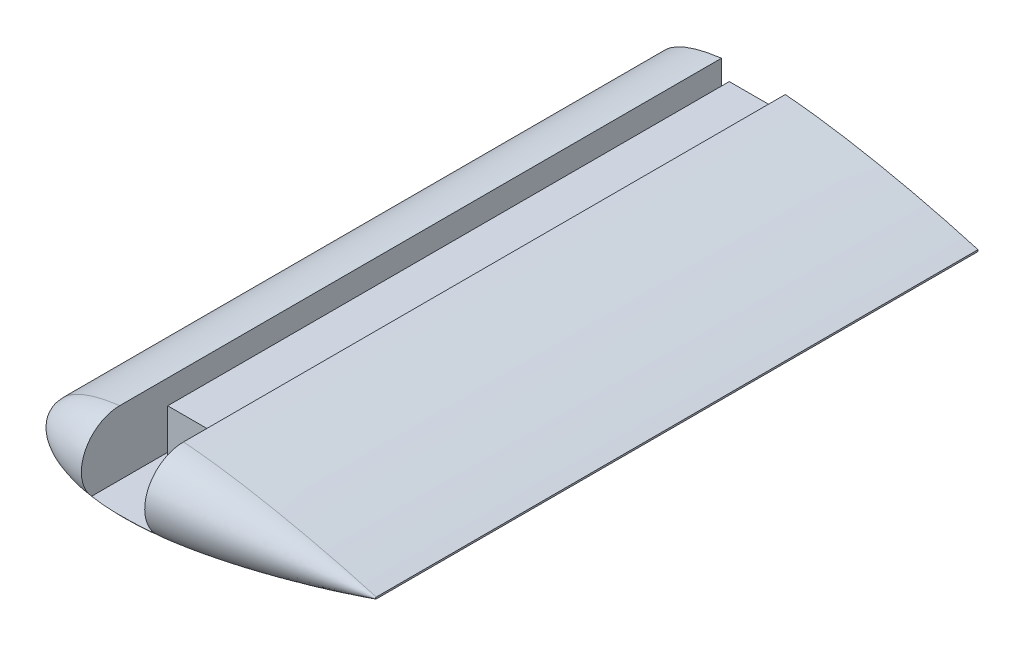
SolidWorks part; units mm, degrees
ref_plane "Спереди" through (0, 0, 0) normal (0, 0, 1) x (1, 0, 0)
ref_plane "Сверху" through (0, 0, 0) normal (0, 1, 0) x (1, 0, 0)
ref_plane "Справа" through (0, 0, 0) normal (1, 0, 0) x (0, 0, -1)
other "Configuration Table"
curve "Curve1"
  spline degree 3 poles (1, 0.0026, 0) (0.9995, 0.0028, 0) (0.9974, 0.0034, 0) (0.9928, 0.0047, 0) (0.9852, 0.0069, 0) (0.9746, 0.01, 0) (0.961, 0.0138, 0) (0.9446, 0.0183, 0) (0.9255, 0.0235, 0) (0.9037, 0.0292, 0) (0.8794, 0.0355, 0) (0.8529, 0.0421, 0) (0.8241, 0.0491, 0) (0.7933, 0.0562, 0) (0.7607, 0.0635, 0) (0.7266, 0.0709, 0) (0.691, 0.0782, 0) (0.6542, 0.0854, 0) (0.6165, 0.0923, 0) (0.5781, 0.0988, 0) (0.5392, 0.1049, 0) (0.5, 0.1104, 0) (0.4609, 0.1152, 0) (0.422, 0.1192, 0) (0.3836, 0.1222, 0) (0.3458, 0.1243, 0) (0.3091, 0.1252, 0) (0.2735, 0.1249, 0) (0.2392, 0.1234, 0) (0.2066, 0.1205, 0) (0.1758, 0.1164, 0) (0.147, 0.111, 0) (0.1203, 0.1043, 0) (0.096, 0.0965, 0) (0.0741, 0.0875, 0) (0.0549, 0.0774, 0) (0.0383, 0.0665, 0) (0.0245, 0.0546, 0) (0.0137, 0.042, 0) (0.0058, 0.0286, 0) (0.001, 0.0145, 0) (-0.0005, 0, 0) (0.001, -0.0145, 0) (0.0058, -0.0286, 0) (0.0137, -0.042, 0) (0.0245, -0.0546, 0) (0.0383, -0.0665, 0) (0.0549, -0.0774, 0) (0.0741, -0.0875, 0) (0.096, -0.0965, 0) (0.1203, -0.1043, 0) (0.147, -0.111, 0) (0.1758, -0.1164, 0) (0.2066, -0.1205, 0) (0.2392, -0.1234, 0) (0.2735, -0.1249, 0) (0.3091, -0.1252, 0) (0.3458, -0.1243, 0) (0.3836, -0.1222, 0) (0.422, -0.1192, 0) (0.4609, -0.1152, 0) (0.5, -0.1104, 0) (0.5392, -0.1049, 0) (0.5781, -0.0988, 0) (0.6165, -0.0923, 0) (0.6542, -0.0854, 0) (0.691, -0.0782, 0) (0.7266, -0.0709, 0) (0.7607, -0.0635, 0) (0.7933, -0.0562, 0) (0.8241, -0.0491, 0) (0.8529, -0.0421, 0) (0.8794, -0.0355, 0) (0.9037, -0.0292, 0) (0.9255, -0.0235, 0) (0.9446, -0.0183, 0) (0.961, -0.0138, 0) (0.9746, -0.01, 0) (0.9852, -0.0069, 0) (0.9928, -0.0047, 0) (0.9974, -0.0034, 0) (0.9995, -0.0028, 0) (1, -0.0026, 0) knots 0 0 0 0 0.000754 0.003013 0.006759 0.011967 0.018601 0.026614 0.035953 0.046555 0.058348 0.071256 0.085193 0.100071 0.115793 0.132259 0.149363 0.166997 0.185048 0.203403 0.221946 0.240561 0.259134 0.27755 0.295701 0.313483 0.330797 0.347552 0.363666 0.379065 0.393686 0.407475 0.420392 0.432406 0.443503 0.453686 0.462984 0.471456 0.479204 0.486388 0.493229 0.5 0.506771 0.513612 0.520796 0.528544 0.537016 0.546314 0.556497 0.567594 0.579608 0.592525 0.606314 0.620935 0.636334 0.652448 0.669203 0.686517 0.704299 0.72245 0.740866 0.759439 0.778054 0.796597 0.814952 0.833003 0.850637 0.867741 0.884207 0.899929 0.914807 0.928744 0.941652 0.953445 0.964047 0.973386 0.981399 0.988033 0.993241 0.996987 0.999246 1 1 1 1
sketch "Sketch2" plane through (0, 0, 0) normal (0, 0, 1) x (1, 0, 0)
  line L0 (55.999, 0.2099) -> (55.999, -0.2099) construction
  line L1 (55.999, 0) -> (-23.9777, 0) construction
  line L2 (-23.9777, 0) -> (-23.9777, 20.1567) construction
  line L3 (-7.5754, 10) -> (21.8908, 10) construction
  line L4 (55.999, 0.2099) -> (55.999, -0.2099)
  line L5 (0, 10) -> (0, -10) construction
  line L6 (55.999, -0.2099) -> (55.999, 14.9208) construction
  spline S1 degree 3 poles (55.999, 0.2099) (53.4639, 0.9505) (48.8039, 2.2339) (42.4289, 3.8199) (36.7434, 5.1209) (31.1997, 6.2872) (25.2824, 7.4075) (20.1765, 8.2452) (14.9796, 8.9749) (10.8215, 9.4486) (6.6974, 9.777) (3.6807, 9.9396) (0.7396, 10.0127) (-2.1078, 9.99) (-4.8439, 9.867) (-7.4522, 9.6409) (-9.9165, 9.3106) (-12.2218, 8.8772) (-14.354, 8.3437) (-16.3004, 7.7143) (-18.0494, 6.9954) (-19.5906, 6.1934) (-20.9154, 5.3156) (-22.0159, 4.3681) (-22.8849, 3.3565) (-23.5145, 2.285) (-23.8954, 1.1588) (-24.0187, 0) (-23.8954, -1.1588) (-23.5145, -2.285) (-22.8849, -3.3565) (-22.0159, -4.3681) (-20.9154, -5.3156) (-19.5906, -6.1934) (-18.0494, -6.9954) (-16.3004, -7.7143) (-14.354, -8.3437) (-12.2218, -8.8772) (-9.9165, -9.3106) (-7.4522, -9.6409) (-4.8439, -9.867) (-2.1078, -9.99) (0.7396, -10.0127) (3.6807, -9.9396) (7.7407, -9.7208) (12.9128, -9.2413) (19.1367, -8.4158) (25.2824, -7.4074) (31.1998, -6.2873) (37.5172, -4.9581) (44.7426, -3.2759) (51.0576, -1.6263) (54.945, -0.5178) (55.9579, -0.2219) (55.999, -0.2099) knots 0 0 0 0 0.046555 0.085193 0.115793 0.149363 0.185048 0.221946 0.240561 0.27755 0.295701 0.313483 0.330797 0.347552 0.363666 0.379065 0.393686 0.407475 0.420392 0.432406 0.443503 0.453686 0.462984 0.471456 0.479204 0.486388 0.493229 0.5 0.506771 0.513612 0.520796 0.528544 0.537016 0.546314 0.556497 0.567594 0.579608 0.592525 0.606314 0.620935 0.636334 0.652448 0.669203 0.686517 0.704299 0.740866 0.778054 0.814952 0.850637 0.884207 0.928744 0.981399 0.999246 1 1 1 1
  point P11 (0, 0)
  dimension "D1" = 20
extrude "Boss-Extrude1" add sketch "Sketch2" along normal blind 150
sketch "Sketch4" plane through (0, 0, 150) normal (0, 0, 1) x (1, 0, 0)
  line L0 (55.999, 0) -> (-23.9777, 0)
  line L1 (55.999, -0.2099) -> (55.999, 0.2099) construction
  line L3 (55.999, -0.2099) -> (55.999, 0.2099)
  line L4 (55.999, 0) -> (55.999, 0.2099)
  spline S0 degree 3 poles (55.999, 0.2099) (53.4639, 0.9505) (48.8039, 2.2339) (42.4289, 3.8199) (36.7434, 5.1209) (31.1997, 6.2872) (25.2824, 7.4075) (20.1765, 8.2452) (14.9796, 8.9749) (10.8215, 9.4486) (6.6974, 9.777) (3.6807, 9.9396) (0.7396, 10.0127) (-2.1078, 9.99) (-4.8439, 9.867) (-7.4522, 9.6409) (-9.9165, 9.3106) (-12.2218, 8.8772) (-14.354, 8.3437) (-16.3004, 7.7143) (-18.0494, 6.9954) (-19.5906, 6.1934) (-20.9154, 5.3156) (-22.0159, 4.3681) (-22.8849, 3.3565) (-23.5145, 2.285) (-23.8954, 1.1588) (-24.0187, 0) (-23.8954, -1.1588) (-23.5145, -2.285) (-22.8849, -3.3565) (-22.0159, -4.3681) (-20.9154, -5.3156) (-19.5906, -6.1934) (-18.0494, -6.9954) (-16.3004, -7.7143) (-14.354, -8.3437) (-12.2218, -8.8772) (-9.9165, -9.3106) (-7.4522, -9.6409) (-4.8439, -9.867) (-2.1078, -9.99) (0.7396, -10.0127) (3.6807, -9.9396) (7.7407, -9.7208) (12.9128, -9.2413) (19.1367, -8.4158) (25.2824, -7.4074) (31.1998, -6.2873) (37.5172, -4.9581) (44.7426, -3.2759) (51.0576, -1.6263) (54.945, -0.5178) (55.9579, -0.2219) (55.999, -0.2099) knots 0 0 0 0 0.046555 0.085193 0.115793 0.149363 0.185048 0.221946 0.240561 0.27755 0.295701 0.313483 0.330797 0.347552 0.363666 0.379065 0.393686 0.407475 0.420392 0.432406 0.443503 0.453686 0.462984 0.471456 0.479204 0.486388 0.493229 0.5 0.506771 0.513612 0.520796 0.528544 0.537016 0.546314 0.556497 0.567594 0.579608 0.592525 0.606314 0.620935 0.636334 0.652448 0.669203 0.686517 0.704299 0.740866 0.778054 0.814952 0.850637 0.884207 0.928744 0.981399 0.999246 1 1 1 1 construction
  spline S2 degree 3 poles (-635.3554, -2880.1705) (392.2047, -313.7808) (246.3383, -46.9116) (42.4289, 3.8199) (36.7434, 5.1209) (31.1997, 6.2872) (25.2824, 7.4075) (20.1765, 8.2452) (14.9796, 8.9749) (10.8215, 9.4486) (6.6974, 9.777) (3.6807, 9.9396) (0.7396, 10.0127) (-2.1078, 9.99) (-4.8439, 9.867) (-7.4522, 9.6409) (-9.9165, 9.3106) (-12.2218, 8.8772) (-14.354, 8.3437) (-16.3004, 7.7143) (-18.0494, 6.9954) (-19.5906, 6.1934) (-20.9154, 5.3156) (-22.0159, 4.3681) (-22.8849, 3.3565) (-23.5145, 2.285) (-23.8954, 1.1588) (-24.0187, 0) (-23.8954, -1.1588) (-23.5145, -2.285) (-22.8849, -3.3565) (-22.0159, -4.3681) (-20.9154, -5.3156) (-19.5906, -6.1934) (-18.0494, -6.9954) (-16.3004, -7.7143) (-14.354, -8.3437) (-12.2218, -8.8772) (-9.9165, -9.3106) (-7.4522, -9.6409) (-4.8439, -9.867) (-2.1078, -9.99) (0.7396, -10.0127) (3.6807, -9.9396) (7.7407, -9.7208) (12.9128, -9.2413) (19.1367, -8.4158) (25.2824, -7.4074) (31.1998, -6.2873) (37.5172, -4.9581) (44.7426, -3.2759) (51.0576, -1.6263) (81.4934, 7.0521) (107.6521, 19.7196) (975.9197, -2854.3918) knots -3.587955 -3.587955 -3.587955 -3.587955 0.046555 0.085193 0.115793 0.149363 0.185048 0.221946 0.240561 0.27755 0.295701 0.313483 0.330797 0.347552 0.363666 0.379065 0.393686 0.407475 0.420392 0.432406 0.443503 0.453686 0.462984 0.471456 0.479204 0.486388 0.493229 0.5 0.506771 0.513612 0.520796 0.528544 0.537016 0.546314 0.556497 0.567594 0.579608 0.592525 0.606314 0.620935 0.636334 0.652448 0.669203 0.686517 0.704299 0.740866 0.778054 0.814952 0.850637 0.884207 0.928744 0.981399 0.999246 1.486622 1.486622 1.486622 1.486622 only from (55.999, 0.2099) to (55.999, -0.2099)
  spline S3 degree 3 poles (55.999, 0.2099) (53.4639, 0.9505) (48.8039, 2.2339) (42.4289, 3.8199) (36.7434, 5.1209) (31.1997, 6.2872) (25.2824, 7.4075) (20.1765, 8.2452) (14.9796, 8.9749) (10.8215, 9.4486) (6.6974, 9.777) (3.6807, 9.9396) (0.7396, 10.0127) (-2.1078, 9.99) (-4.8439, 9.867) (-7.4522, 9.6409) (-9.9165, 9.3106) (-12.2218, 8.8772) (-14.354, 8.3437) (-16.3004, 7.7143) (-18.0494, 6.9954) (-19.5906, 6.1934) (-20.9154, 5.3156) (-22.0159, 4.3681) (-22.8849, 3.3565) (-23.5145, 2.285) (-23.8954, 1.1588) (-23.9777, 0.3849) (-23.9777, 0) knots 0 0 0 0 0.046555 0.085193 0.115793 0.149363 0.185048 0.221946 0.240561 0.27755 0.295701 0.313483 0.330797 0.347552 0.363666 0.379065 0.393686 0.407475 0.420392 0.432406 0.443503 0.453686 0.462984 0.471456 0.479204 0.486388 0.493229 0.5 0.5 0.5 0.5
  dimension "D1" = 0
revolve "Revolve1" add sketch "Sketch4" angle 180 about L0
sketch "Sketch3" plane through (0, 0, 0) normal (0, 0, -1) x (-1, 0, 0)
  line L0 (6, -6.5) -> (7.95, -6.5)
  line L2 (-6, -6.5) -> (-6, 5.5)
  line L3 (-6, 5.5) -> (6, 5.5)
  line L4 (6, -6.5) -> (6, 5.5)
  line L5 (-6, -6.5) -> (6, 5.5) construction
  line L6 (-6, 5.5) -> (6, -6.5) construction
  line L7 (7.95, -6.5) -> (7.95, 9.5637)
  line L8 (-6, -6.5) -> (-7.95, -6.5)
  line L9 (-7.95, -6.5) -> (-7.95, 9.6738)
  line L10 (-11.2468, 10) -> (11.5184, 10) construction
  line L11 (0, 0) -> (0, 6.0357) construction
  line L12 (-7.95, -6.5) -> (7.95, -6.5) construction
  spline S0 degree 3 poles (275.2851, -1947.3186) (-351.5026, -245.2226) (-218.8463, -40.0718) (-42.4289, 3.8199) (-36.7434, 5.1209) (-31.1997, 6.2872) (-25.2824, 7.4075) (-20.1765, 8.2452) (-14.9796, 8.9749) (-10.8215, 9.4486) (-6.6974, 9.777) (-3.6807, 9.9396) (-0.7396, 10.0127) (2.1078, 9.99) (4.8439, 9.867) (7.4522, 9.6409) (9.9165, 9.3106) (12.2218, 8.8772) (14.354, 8.3437) (16.3004, 7.7143) (18.0494, 6.9954) (19.5906, 6.1934) (20.9154, 5.3156) (22.0159, 4.3681) (22.8849, 3.3565) (23.5145, 2.285) (23.8954, 1.1588) (24.0187, 0) (23.8954, -1.1588) (23.5145, -2.285) (22.8849, -3.3565) (22.0159, -4.3681) (20.9154, -5.3156) (19.5906, -6.1934) (18.0494, -6.9954) (16.3004, -7.7143) (14.354, -8.3437) (12.2218, -8.8772) (9.9165, -9.3106) (7.4522, -9.6409) (4.8439, -9.867) (2.1078, -9.99) (-0.7396, -10.0127) (-3.6807, -9.9396) (-7.7407, -9.7208) (-12.9128, -9.2413) (-19.1367, -8.4158) (-25.2824, -7.4074) (-31.1998, -6.2873) (-37.5172, -4.9581) (-44.7426, -3.2759) (-51.0576, -1.6263) (-78.1348, 6.0944) (-101.2564, 16.704) (-685.5525, -1897.6172) knots -3.088599 -3.088599 -3.088599 -3.088599 0.046555 0.085193 0.115793 0.149363 0.185048 0.221946 0.240561 0.27755 0.295701 0.313483 0.330797 0.347552 0.363666 0.379065 0.393686 0.407475 0.420392 0.432406 0.443503 0.453686 0.462984 0.471456 0.479204 0.486388 0.493229 0.5 0.506771 0.513612 0.520796 0.528544 0.537016 0.546314 0.556497 0.567594 0.579608 0.592525 0.606314 0.620935 0.636334 0.652448 0.669203 0.686517 0.704299 0.740866 0.778054 0.814952 0.850637 0.884207 0.928744 0.981399 0.999246 1.425061 1.425061 1.425061 1.425061 only from (-55.999, 0.2099) to (-55.999, -0.2099) construction
  spline S1 degree 3 poles (-7.95, 9.6738) (-7.5253, 9.7065) (-6.0943, 9.8095) (-3.6807, 9.9396) (-0.7396, 10.0127) (2.1078, 9.99) (4.8439, 9.867) (6.7781, 9.6993) (7.7981, 9.5819) (7.95, 9.5637) knots 0.288193 0.288193 0.288193 0.288193 0.295701 0.313483 0.330797 0.347552 0.363666 0.379065 0.381762 0.381762 0.381762 0.381762
  point P0 (0, -0.5)
  point P13 (-6.975, -6.5)
  dimension "D1" = 12
  dimension "D2" = 12
  dimension "D3" = 1.95
  dimension "D4" = 1.95
  dimension "D5" = 16.5
extrude "Cut-Extrude1" cut sketch "Sketch3" against normal up to next
ref_plane "Plane1" through (0, 0, 140) normal (0, 0, -1) x (-1, 0, 0)
sketch "Sketch5" plane through (0, 0, 140) normal (0, 0, -1) x (-1, 0, 0)
  line L1 (-7.95, -6.5) -> (7.95, -6.5)
  line L2 (-7.95, -6.5) -> (-7.95, 9.5637)
  line L3 (-7.95, 9.5637) -> (7.95, 9.5637)
  line L4 (7.95, -6.5) -> (7.95, 9.5637)
extrude "Cut-Extrude2" cut sketch "Sketch5" against normal up to next
